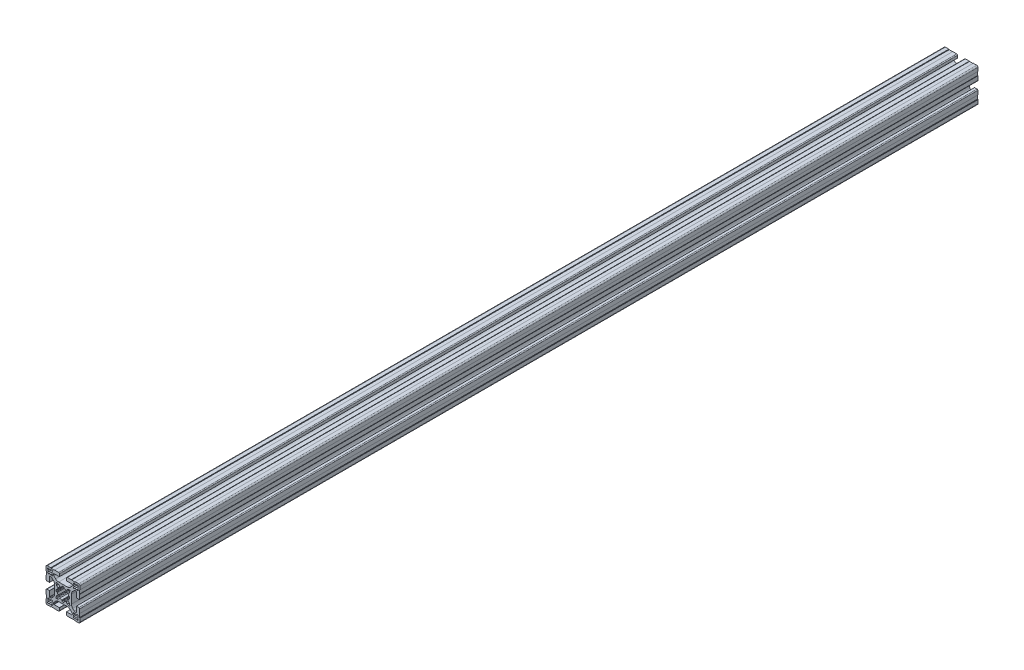
SolidWorks part; units mm, degrees
ref_plane "Plano frontal" through (0, 0, 0) normal (0, 0, 1) x (1, 0, 0)
ref_plane "Plano superior" through (0, 0, 0) normal (0, 1, 0) x (1, 0, 0)
ref_plane "Plano direito" through (0, 0, 0) normal (1, 0, 0) x (0, 0, -1)
sketch "Esboço1" plane through (0, 0, 0) normal (0, 0, 1) x (1, 0, 0)
  line B0 (-17.8572, 16.7966) -> (-17.4167, 16.356)
  arc B1 (-16.7966, 17.8572) -> (-17.8572, 16.7966) centre (-17.3269, 17.3269) ccw
  line B2 (-16.356, 17.4167) -> (-16.7966, 17.8572)
  arc B3 (-14.044, 17.4167) -> (-16.356, 17.4167) centre (-15.2, 15.2) ccw
  line B4 (-13.6034, 17.8572) -> (-14.044, 17.4167)
  arc B5 (-12.5428, 16.7966) -> (-13.6034, 17.8572) centre (-13.0731, 17.3269) ccw
  line B6 (-12.9833, 16.356) -> (-12.5428, 16.7966)
  arc B7 (-12.9833, 14.044) -> (-12.9833, 16.356) centre (-15.2, 15.2) ccw
  line B8 (-12.5428, 13.6034) -> (-12.9833, 14.044)
  arc B9 (-13.6034, 12.5428) -> (-12.5428, 13.6034) centre (-13.0731, 13.0731) ccw
  line B10 (-14.044, 12.9833) -> (-13.6034, 12.5428)
  arc B11 (-16.356, 12.9833) -> (-14.044, 12.9833) centre (-15.2, 15.2) ccw
  line B12 (-16.7966, 12.5428) -> (-16.356, 12.9833)
  arc B13 (-17.8572, 13.6034) -> (-16.7966, 12.5428) centre (-17.3269, 13.0731) ccw
  line B14 (-17.4167, 14.044) -> (-17.8572, 13.6034)
  arc B15 (-17.4167, 16.356) -> (-17.4167, 14.044) centre (-15.2, 15.2) ccw
  line B16 (17.4167, 14.044) -> (17.8572, 13.6034)
  arc B17 (16.7966, 12.5428) -> (17.8572, 13.6034) centre (17.3269, 13.0731) ccw
  line B18 (16.7966, 12.5428) -> (16.356, 12.9833)
  arc B19 (14.044, 12.9833) -> (16.356, 12.9833) centre (15.2, 15.2) ccw
  line B20 (14.044, 12.9833) -> (13.6034, 12.5428)
  arc B21 (12.5428, 13.6034) -> (13.6034, 12.5428) centre (13.0731, 13.0731) ccw
  line B22 (12.5428, 13.6034) -> (12.9833, 14.044)
  arc B23 (12.9833, 16.356) -> (12.9833, 14.044) centre (15.2, 15.2) ccw
  line B24 (12.9833, 16.356) -> (12.5428, 16.7966)
  arc B25 (13.6034, 17.8572) -> (12.5428, 16.7966) centre (13.0731, 17.3269) ccw
  line B26 (13.6034, 17.8572) -> (14.044, 17.4167)
  arc B27 (16.356, 17.4167) -> (14.044, 17.4167) centre (15.2, 15.2) ccw
  line B28 (16.356, 17.4167) -> (16.7966, 17.8572)
  arc B29 (17.8572, 16.7966) -> (16.7966, 17.8572) centre (17.3269, 17.3269) ccw
  line B30 (17.8572, 16.7966) -> (17.4167, 16.356)
  arc B31 (17.4167, 14.044) -> (17.4167, 16.356) centre (15.2, 15.2) ccw
  line B32 (-17.4167, -14.044) -> (-17.8572, -13.6034)
  arc B33 (-16.7966, -12.5428) -> (-17.8572, -13.6034) centre (-17.3269, -13.0731) ccw
  line B34 (-16.7966, -12.5428) -> (-16.356, -12.9833)
  arc B35 (-14.044, -12.9833) -> (-16.356, -12.9833) centre (-15.2, -15.2) ccw
  line B36 (-14.044, -12.9833) -> (-13.6034, -12.5428)
  arc B37 (-12.5428, -13.6034) -> (-13.6034, -12.5428) centre (-13.0731, -13.0731) ccw
  line B38 (-12.5428, -13.6034) -> (-12.9833, -14.044)
  arc B39 (-12.9833, -16.356) -> (-12.9833, -14.044) centre (-15.2, -15.2) ccw
  line B40 (-12.9833, -16.356) -> (-12.5428, -16.7966)
  arc B41 (-13.6034, -17.8572) -> (-12.5428, -16.7966) centre (-13.0731, -17.3269) ccw
  line B42 (-13.6034, -17.8572) -> (-14.044, -17.4167)
  arc B43 (-16.356, -17.4167) -> (-14.044, -17.4167) centre (-15.2, -15.2) ccw
  line B44 (-16.356, -17.4167) -> (-16.7966, -17.8572)
  arc B45 (-17.8572, -16.7966) -> (-16.7966, -17.8572) centre (-17.3269, -17.3269) ccw
  line B46 (-17.8572, -16.7966) -> (-17.4167, -16.356)
  arc B47 (-17.4167, -14.044) -> (-17.4167, -16.356) centre (-15.2, -15.2) ccw
  line B48 (17.8572, -16.7966) -> (17.4167, -16.356)
  arc B49 (16.7966, -17.8572) -> (17.8572, -16.7966) centre (17.3269, -17.3269) ccw
  line B50 (16.356, -17.4167) -> (16.7966, -17.8572)
  arc B51 (14.044, -17.4167) -> (16.356, -17.4167) centre (15.2, -15.2) ccw
  line B52 (13.6034, -17.8572) -> (14.044, -17.4167)
  arc B53 (12.5428, -16.7966) -> (13.6034, -17.8572) centre (13.0731, -17.3269) ccw
  line B54 (12.9833, -16.356) -> (12.5428, -16.7966)
  arc B55 (12.9833, -14.044) -> (12.9833, -16.356) centre (15.2, -15.2) ccw
  line B56 (12.5428, -13.6034) -> (12.9833, -14.044)
  arc B57 (13.6034, -12.5428) -> (12.5428, -13.6034) centre (13.0731, -13.0731) ccw
  line B58 (14.044, -12.9833) -> (13.6034, -12.5428)
  arc B59 (16.356, -12.9833) -> (14.044, -12.9833) centre (15.2, -15.2) ccw
  line B60 (16.7966, -12.5428) -> (16.356, -12.9833)
  arc B61 (17.8572, -13.6034) -> (16.7966, -12.5428) centre (17.3269, -13.0731) ccw
  line B62 (17.4167, -14.044) -> (17.8572, -13.6034)
  arc B63 (17.4167, -16.356) -> (17.4167, -14.044) centre (15.2, -15.2) ccw
  line B64 (4.15, -18.8) -> (4.15, -15.9)
  arc B65 (4.25, -15.8) -> (4.15, -15.9) centre (4.25, -15.9) ccw
  line B66 (4.25, -15.8) -> (10.5, -15.8)
  arc B67 (10.5, -15.8) -> (11, -15.3) centre (10.5, -15.3) ccw
  line B68 (11, -15.3) -> (11, -14.4497)
  arc B69 (11, -14.4497) -> (10.5607, -13.3891) centre (9.5, -14.4497) ccw
  line B70 (10.5607, -13.3891) -> (8.636, -11.4645)
  arc B71 (8.636, -11.4645) -> (5.1005, -10) centre (5.1005, -15) ccw
  line B72 (5.1005, -10) -> (0, -10)
  line B73 (0, -10) -> (-5.1005, -10)
  arc B74 (-5.1005, -10) -> (-8.636, -11.4645) centre (-5.1005, -15) ccw
  line B75 (-8.636, -11.4645) -> (-10.5607, -13.3891)
  arc B76 (-10.5607, -13.3891) -> (-11, -14.4497) centre (-9.5, -14.4497) ccw
  line B77 (-11, -14.4497) -> (-11, -15.3)
  arc B78 (-11, -15.3) -> (-10.5, -15.8) centre (-10.5, -15.3) ccw
  line B79 (-10.5, -15.8) -> (-4.25, -15.8)
  arc B80 (-4.15, -15.9) -> (-4.25, -15.8) centre (-4.25, -15.9) ccw
  line B81 (-4.15, -15.9) -> (-4.15, -18.8)
  arc B82 (-5.15, -19.8) -> (-4.15, -18.8) centre (-5.15, -18.8) ccw
  line B83 (-5.15, -19.8) -> (-9.8, -19.8)
  line B84 (-9.8, -19.8) -> (-10, -19.6)
  line B85 (-10, -19.6) -> (-14, -19.6)
  line B86 (-14, -19.6) -> (-14.4, -20)
  line B87 (-14.4, -20) -> (-18.5, -20)
  arc B88 (-20, -18.5) -> (-18.5, -20) centre (-18.5, -18.5) ccw
  line B89 (-20, -18.5) -> (-20, -14.4)
  line B90 (-20, -14.4) -> (-19.6, -14)
  line B91 (-19.6, -14) -> (-19.6, -10)
  line B92 (-19.6, -10) -> (-19.8, -9.8)
  line B93 (-19.8, -9.8) -> (-19.8, -5.15)
  arc B94 (-18.8, -4.15) -> (-19.8, -5.15) centre (-18.8, -5.15) ccw
  line B95 (-18.8, -4.15) -> (-15.9, -4.15)
  arc B96 (-15.8, -4.25) -> (-15.9, -4.15) centre (-15.9, -4.25) ccw
  line B97 (-15.8, -4.25) -> (-15.8, -10.5)
  arc B98 (-15.8, -10.5) -> (-15.3, -11) centre (-15.3, -10.5) ccw
  line B99 (-15.3, -11) -> (-14.4497, -11)
  arc B100 (-14.4497, -11) -> (-13.3891, -10.5607) centre (-14.4497, -9.5) ccw
  line B101 (-13.3891, -10.5607) -> (-11.4645, -8.636)
  arc B102 (-11.4645, -8.636) -> (-10, -5.1005) centre (-15, -5.1005) ccw
  line B103 (-10, -5.1005) -> (-10, 0)
  line B104 (-10, 0) -> (-10, 5.1005)
  arc B105 (-10, 5.1005) -> (-11.4645, 8.636) centre (-15, 5.1005) ccw
  line B106 (-11.4645, 8.636) -> (-13.3891, 10.5607)
  arc B107 (-13.3891, 10.5607) -> (-14.4497, 11) centre (-14.4497, 9.5) ccw
  line B108 (-14.4497, 11) -> (-15.3, 11)
  arc B109 (-15.3, 11) -> (-15.8, 10.5) centre (-15.3, 10.5) ccw
  line B110 (-15.8, 10.5) -> (-15.8, 4.25)
  arc B111 (-15.9, 4.15) -> (-15.8, 4.25) centre (-15.9, 4.25) ccw
  line B112 (-15.9, 4.15) -> (-18.8, 4.15)
  arc B113 (-19.8, 5.15) -> (-18.8, 4.15) centre (-18.8, 5.15) ccw
  line B114 (-19.8, 5.15) -> (-19.8, 9.8)
  line B115 (-19.8, 9.8) -> (-19.6, 10)
  line B116 (-19.6, 10) -> (-19.6, 14)
  line B117 (-19.6, 14) -> (-20, 14.4)
  line B118 (-20, 14.4) -> (-20, 18.5)
  arc B119 (-18.5, 20) -> (-20, 18.5) centre (-18.5, 18.5) ccw
  line B120 (-18.5, 20) -> (-14.4, 20)
  line B121 (-14.4, 20) -> (-14, 19.6)
  line B122 (-14, 19.6) -> (-10, 19.6)
  line B123 (-10, 19.6) -> (-9.8, 19.8)
  line B124 (-9.8, 19.8) -> (-5.15, 19.8)
  arc B125 (-4.15, 18.8) -> (-5.15, 19.8) centre (-5.15, 18.8) ccw
  line B126 (-4.15, 18.8) -> (-4.15, 15.9)
  arc B127 (-4.25, 15.8) -> (-4.15, 15.9) centre (-4.25, 15.9) ccw
  line B128 (-4.25, 15.8) -> (-10.5, 15.8)
  arc B129 (-10.5, 15.8) -> (-11, 15.3) centre (-10.5, 15.3) ccw
  line B130 (-11, 15.3) -> (-11, 14.4497)
  arc B131 (-11, 14.4497) -> (-10.5607, 13.3891) centre (-9.5, 14.4497) ccw
  line B132 (-10.5607, 13.3891) -> (-8.636, 11.4645)
  arc B133 (-8.636, 11.4645) -> (-5.1005, 10) centre (-5.1005, 15) ccw
  line B134 (-5.1005, 10) -> (0, 10)
  line B135 (0, 10) -> (5.1005, 10)
  arc B136 (5.1005, 10) -> (8.636, 11.4645) centre (5.1005, 15) ccw
  line B137 (8.636, 11.4645) -> (10.5607, 13.3891)
  arc B138 (10.5607, 13.3891) -> (11, 14.4497) centre (9.5, 14.4497) ccw
  line B139 (11, 14.4497) -> (11, 15.3)
  arc B140 (11, 15.3) -> (10.5, 15.8) centre (10.5, 15.3) ccw
  line B141 (10.5, 15.8) -> (4.25, 15.8)
  arc B142 (4.15, 15.9) -> (4.25, 15.8) centre (4.25, 15.9) ccw
  line B143 (4.15, 15.9) -> (4.15, 18.8)
  arc B144 (5.15, 19.8) -> (4.15, 18.8) centre (5.15, 18.8) ccw
  line B145 (5.15, 19.8) -> (9.8, 19.8)
  line B146 (9.8, 19.8) -> (10, 19.6)
  line B147 (10, 19.6) -> (14, 19.6)
  line B148 (14, 19.6) -> (14.4, 20)
  line B149 (14.4, 20) -> (18.5, 20)
  arc B150 (20, 18.5) -> (18.5, 20) centre (18.5, 18.5) ccw
  line B151 (20, 18.5) -> (20, 14.4)
  line B152 (20, 14.4) -> (19.6, 14)
  line B153 (19.6, 14) -> (19.6, 10)
  line B154 (19.6, 10) -> (19.8, 9.8)
  line B155 (19.8, 9.8) -> (19.8, 5.15)
  arc B156 (18.8, 4.15) -> (19.8, 5.15) centre (18.8, 5.15) ccw
  line B157 (18.8, 4.15) -> (15.9, 4.15)
  arc B158 (15.8, 4.25) -> (15.9, 4.15) centre (15.9, 4.25) ccw
  line B159 (15.8, 4.25) -> (15.8, 10.5)
  arc B160 (15.8, 10.5) -> (15.3, 11) centre (15.3, 10.5) ccw
  line B161 (15.3, 11) -> (14.4497, 11)
  arc B162 (14.4497, 11) -> (13.3891, 10.5607) centre (14.4497, 9.5) ccw
  line B163 (13.3891, 10.5607) -> (11.4645, 8.636)
  arc B164 (11.4645, 8.636) -> (10, 5.1005) centre (15, 5.1005) ccw
  line B165 (10, 5.1005) -> (10, 0)
  line B166 (10, 0) -> (10, -5.1005)
  arc B167 (10, -5.1005) -> (11.4645, -8.636) centre (15, -5.1005) ccw
  line B168 (11.4645, -8.636) -> (13.3891, -10.5607)
  arc B169 (13.3891, -10.5607) -> (14.4497, -11) centre (14.4497, -9.5) ccw
  line B170 (14.4497, -11) -> (15.3, -11)
  arc B171 (15.3, -11) -> (15.8, -10.5) centre (15.3, -10.5) ccw
  line B172 (15.8, -10.5) -> (15.8, -4.25)
  arc B173 (15.9, -4.15) -> (15.8, -4.25) centre (15.9, -4.25) ccw
  line B174 (15.9, -4.15) -> (18.8, -4.15)
  arc B175 (19.8, -5.15) -> (18.8, -4.15) centre (18.8, -5.15) ccw
  line B176 (19.8, -5.15) -> (19.8, -9.8)
  line B177 (19.8, -9.8) -> (19.6, -10)
  line B178 (19.6, -10) -> (19.6, -14)
  line B179 (19.6, -14) -> (20, -14.4)
  line B180 (20, -14.4) -> (20, -18.5)
  arc B181 (18.5, -20) -> (20, -18.5) centre (18.5, -18.5) ccw
  line B182 (18.5, -20) -> (14.4, -20)
  line B183 (14.4, -20) -> (14, -19.6)
  line B184 (14, -19.6) -> (10, -19.6)
  line B185 (10, -19.6) -> (9.8, -19.8)
  line B186 (9.8, -19.8) -> (5.15, -19.8)
  arc B187 (4.15, -18.8) -> (5.15, -19.8) centre (5.15, -18.8) ccw
  line B188 (-5.3139, -7.6355) -> (-7.6488, -8.2611)
  arc B189 (-8.2611, -7.6488) -> (-7.6488, -8.2611) centre (-7.7782, -7.7782) ccw
  line B190 (-8.2611, -7.6488) -> (-7.6355, -5.3139)
  arc B191 (-7.4569, -5.0466) -> (-7.6355, -5.3139) centre (-7.1525, -5.4433) ccw
  line B192 (-7.4569, -5.0466) -> (-5.744, -3.7322)
  arc B193 (-6.7007, -1.4225) -> (-5.744, -3.7322) centre (0, 0) ccw
  line B194 (-6.7007, -1.4225) -> (-7.5204, -1.3146)
  arc B195 (-7.9522, -0.8735) -> (-7.5204, -1.3146) centre (-7.4552, -0.8189) ccw
  arc B196 (-7.9522, 0.8735) -> (-7.9522, -0.8735) centre (0, 0) ccw
  arc B197 (-7.5204, 1.3146) -> (-7.9522, 0.8735) centre (-7.4552, 0.8189) ccw
  line B198 (-7.5204, 1.3146) -> (-6.7007, 1.4225)
  arc B199 (-5.744, 3.7322) -> (-6.7007, 1.4225) centre (0, 0) ccw
  line B200 (-5.744, 3.7322) -> (-7.4569, 5.0466)
  arc B201 (-7.6355, 5.3139) -> (-7.4569, 5.0466) centre (-7.1525, 5.4433) ccw
  line B202 (-7.6355, 5.3139) -> (-8.2611, 7.6488)
  arc B203 (-7.6488, 8.2611) -> (-8.2611, 7.6488) centre (-7.7782, 7.7782) ccw
  line B204 (-7.6488, 8.2611) -> (-5.3139, 7.6355)
  arc B205 (-5.0466, 7.4569) -> (-5.3139, 7.6355) centre (-5.4433, 7.1525) ccw
  line B206 (-5.0466, 7.4569) -> (-3.7322, 5.744)
  arc B207 (-1.4225, 6.7007) -> (-3.7322, 5.744) centre (0, 0) ccw
  line B208 (-1.4225, 6.7007) -> (-1.3146, 7.5204)
  arc B209 (-0.8735, 7.9522) -> (-1.3146, 7.5204) centre (-0.8189, 7.4552) ccw
  arc B210 (0.8735, 7.9522) -> (-0.8735, 7.9522) centre (0, 0) ccw
  arc B211 (1.3146, 7.5204) -> (0.8735, 7.9522) centre (0.8189, 7.4552) ccw
  line B212 (1.3146, 7.5204) -> (1.4225, 6.7007)
  arc B213 (3.7322, 5.744) -> (1.4225, 6.7007) centre (0, 0) ccw
  line B214 (3.7322, 5.744) -> (5.0466, 7.4569)
  arc B215 (5.3139, 7.6355) -> (5.0466, 7.4569) centre (5.4433, 7.1525) ccw
  line B216 (5.3139, 7.6355) -> (7.6488, 8.2611)
  arc B217 (8.2611, 7.6488) -> (7.6488, 8.2611) centre (7.7782, 7.7782) ccw
  line B218 (8.2611, 7.6488) -> (7.6355, 5.3139)
  arc B219 (7.4569, 5.0466) -> (7.6355, 5.3139) centre (7.1525, 5.4433) ccw
  line B220 (7.4569, 5.0466) -> (5.744, 3.7322)
  arc B221 (6.7007, 1.4225) -> (5.744, 3.7322) centre (0, 0) ccw
  line B222 (6.7007, 1.4225) -> (7.5204, 1.3146)
  arc B223 (7.9522, 0.8735) -> (7.5204, 1.3146) centre (7.4552, 0.8189) ccw
  arc B224 (7.9522, -0.8735) -> (7.9522, 0.8735) centre (0, 0) ccw
  arc B225 (7.5204, -1.3146) -> (7.9522, -0.8735) centre (7.4552, -0.8189) ccw
  line B226 (7.5204, -1.3146) -> (6.7007, -1.4225)
  arc B227 (5.744, -3.7322) -> (6.7007, -1.4225) centre (0, 0) ccw
  line B228 (5.744, -3.7322) -> (7.4569, -5.0466)
  arc B229 (7.6355, -5.3139) -> (7.4569, -5.0466) centre (7.1525, -5.4433) ccw
  line B230 (7.6355, -5.3139) -> (8.2611, -7.6488)
  arc B231 (7.6488, -8.2611) -> (8.2611, -7.6488) centre (7.7782, -7.7782) ccw
  line B232 (7.6488, -8.2611) -> (5.3139, -7.6355)
  arc B233 (5.0466, -7.4569) -> (5.3139, -7.6355) centre (5.4433, -7.1525) ccw
  line B234 (5.0466, -7.4569) -> (3.7322, -5.744)
  arc B235 (1.4225, -6.7007) -> (3.7322, -5.744) centre (0, 0) ccw
  line B236 (1.4225, -6.7007) -> (1.3146, -7.5204)
  arc B237 (0.8735, -7.9522) -> (1.3146, -7.5204) centre (0.8189, -7.4552) ccw
  arc B238 (-0.8735, -7.9522) -> (0.8735, -7.9522) centre (0, 0) ccw
  arc B239 (-1.3146, -7.5204) -> (-0.8735, -7.9522) centre (-0.8189, -7.4552) ccw
  line B240 (-1.3146, -7.5204) -> (-1.4225, -6.7007)
  arc B241 (-3.7322, -5.744) -> (-1.4225, -6.7007) centre (0, 0) ccw
  line B242 (-3.7322, -5.744) -> (-5.0466, -7.4569)
  arc B243 (-5.3139, -7.6355) -> (-5.0466, -7.4569) centre (-5.4433, -7.1525) ccw
sketch_block_instance "P40103-1"
sketch_block "P40103"
other "Item de detalhe3"
other "Item de detalhe4"
extrude "Ressalto-extrusão1" add sketch "Esboço1" along normal mid plane 1060
